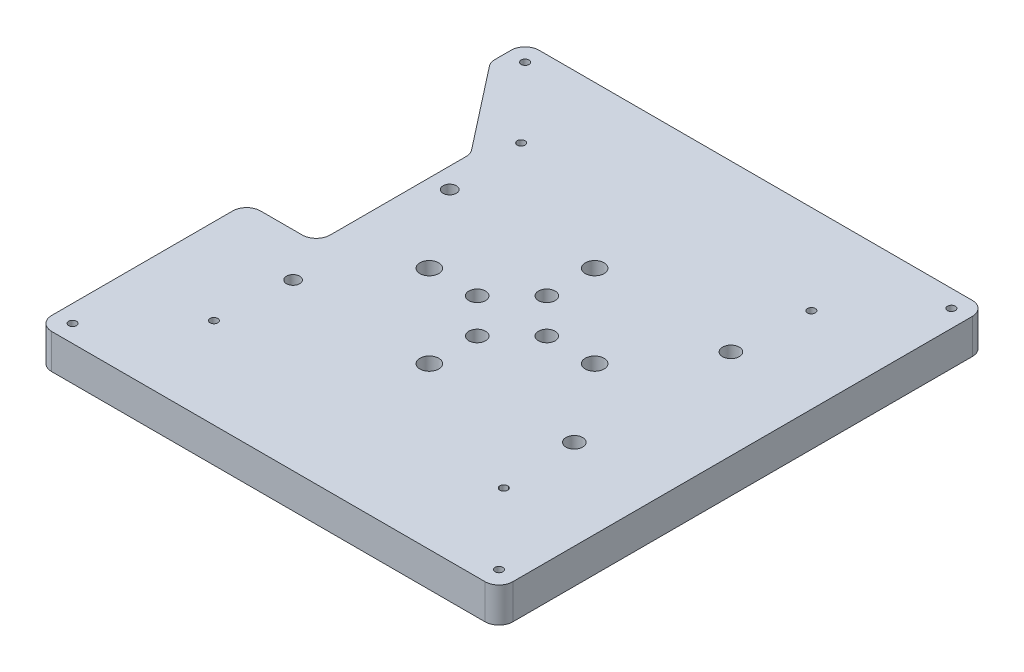
SolidWorks part; units mm, degrees
ref_plane "Front Plane" through (0, 0, 0) normal (0, 0, 1) x (1, 0, 0)
ref_plane "Top Plane" through (0, 0, 0) normal (0, 1, 0) x (1, 0, 0)
ref_plane "Right Plane" through (0, 0, 0) normal (1, 0, 0) x (0, 0, -1)
sketch "Sketch2" plane through (0, 0, 0) normal (0, 1, 0) x (1, 0, 0)
  line L0 (0, 6.35) -> (168.275, 6.35) construction
  line L1 (161.925, 177.8) -> (161.925, 0) construction
  line L2 (0, 88.9) -> (168.275, 88.9) construction
  line L3 (32.8295, 117.475) -> (135.4455, 117.475) construction
  line L8 (32.8295, 117.475) -> (32.8295, 60.325) construction
  line L9 (0, 177.8) -> (168.275, 177.8)
  line L10 (0, 177.8) -> (0, 0)
  line L11 (0, 0) -> (168.275, 0)
  line L12 (168.275, 177.8) -> (168.275, 0)
  line L13 (32.8295, 60.325) -> (135.4455, 60.325) construction
  line L14 (135.4455, 117.475) -> (135.4455, 60.325) construction
  line L15 (84.1375, 177.8) -> (84.1375, 0) construction
  line L16 (6.35, 0) -> (6.35, 177.8) construction
  line L21 (0, 171.45) -> (168.275, 171.45) construction
  line L22 (0, 177.8) -> (168.275, 0) construction
  line L23 (168.275, 177.8) -> (0, 0) construction
  line L24 (31.2511, 144.78) -> (31.2511, 145.2372) construction
  line L25 (31.2511, 144.78) -> (137.0239, 144.78) construction
  line L26 (31.2511, 144.78) -> (31.2511, 33.02) construction
  line L27 (31.2511, 33.02) -> (137.0239, 33.02) construction
  line L28 (137.0239, 144.78) -> (137.0239, 33.02) construction
  line L29 (31.2511, 145.2372) -> (31.1495, 145.2372) construction
  line L30 (137.0239, 144.78) -> (137.0239, 145.161) construction
  line L31 (137.0239, 145.161) -> (137.1255, 145.161) construction
  circle A0 centre (84.1375, 88.9) radius 12.7 construction
  circle A1 centre (84.1375, 101.6) radius 3.048
  circle A2 centre (96.8375, 88.9) radius 3.048
  circle A3 centre (84.1375, 76.2) radius 3.048
  circle A4 centre (71.4375, 88.9) radius 3.048
  circle A5 centre (32.8295, 117.475) radius 2.413
  circle A6 centre (135.4455, 117.475) radius 3.048
  circle A7 centre (135.4455, 60.325) radius 3.048
  circle A8 centre (32.8295, 60.325) radius 2.413
  circle A9 centre (6.35, 171.45) radius 1.4224
  circle A10 centre (161.925, 171.45) radius 1.4224
  circle A11 centre (161.925, 6.35) radius 1.4224
  circle A12 centre (6.35, 6.35) radius 1.4224
  circle A13 centre (31.2511, 33.02) radius 1.4224
  circle A14 centre (137.0239, 144.78) radius 1.4224 construction
  circle A15 centre (31.2511, 144.78) radius 1.4224 construction
  circle A16 centre (137.0239, 33.02) radius 1.4224
  circle A17 centre (84.1375, 88.9) radius 30.1625 construction
  circle A18 centre (84.1375, 119.0625) radius 3.429
  circle A19 centre (114.3, 88.9) radius 3.429
  circle A20 centre (84.1375, 58.7375) radius 3.429
  circle A21 centre (53.975, 88.9) radius 3.429
  circle A22 centre (31.1495, 145.2372) radius 1.4224
  circle A24 centre (137.1255, 145.161) radius 1.4224
  point P19 (135.4455, 88.9)
  point P24 (84.1375, 117.475)
  point P63 (84.1375, 88.9)
  dimension "D3" = 25.4
  dimension "D6" = 2.8448
  dimension "D12" = 60.325
  dimension "D13" = 6.858
  dimension "D14" = 6.096
  dimension "D15" = 6.096
  dimension "D18" = 4.826
  dimension "D1" = 168.275
  dimension "D2" = 177.8
  dimension "D4" = 102.616
  dimension "D5" = 57.15
  dimension "D7" = 6.35
  dimension "D8" = 6.35
  dimension "D9" = 6.35
  dimension "D10" = 6.35
  dimension "D11" = 111.76
  dimension "D16" = 0.4572
  dimension "D17" = 0.381
  dimension "D19" = 0.1016
  dimension "D20" = 0.1016
extrude "Boss-Extrude2" add sketch "Sketch2" along normal blind 12.7
sketch "Sketch3" plane through (0, 12.7, 0) normal (0, 1, 0) x (1, 0, 0)
  line L2 (0, 165.1) -> (0, 76.2)
  line L3 (0, 76.2) -> (25.4, 76.2)
  line L4 (25.4, 132.5895) -> (25.4, 76.2)
  line L5 (0, 165.1) -> (25.4, 132.5895)
  line L6 (168.275, 177.8) -> (0, 177.8) construction
  line L8 (0, 177.8) -> (0, 0) construction
  dimension "D1" = 12.7
  dimension "D2" = 25.4
  dimension "D3" = 88.9
  dimension "D4" = 38
extrude "Cut-Extrude1" cut sketch "Sketch3" against normal through all both and the other way through all contours L4 L3 L2 L5
fillet "Fillet1" radius 5.08 8 edges at (168.275, 6.35, -177.8) (168.275, 6.35, 0) (0, 6.35, 0) (0, 6.35, -177.8) (0, 6.35, -76.2) (0, 6.35, -165.1) (25.4, 6.35, -132.5895) (25.4, 6.35, -76.2)
